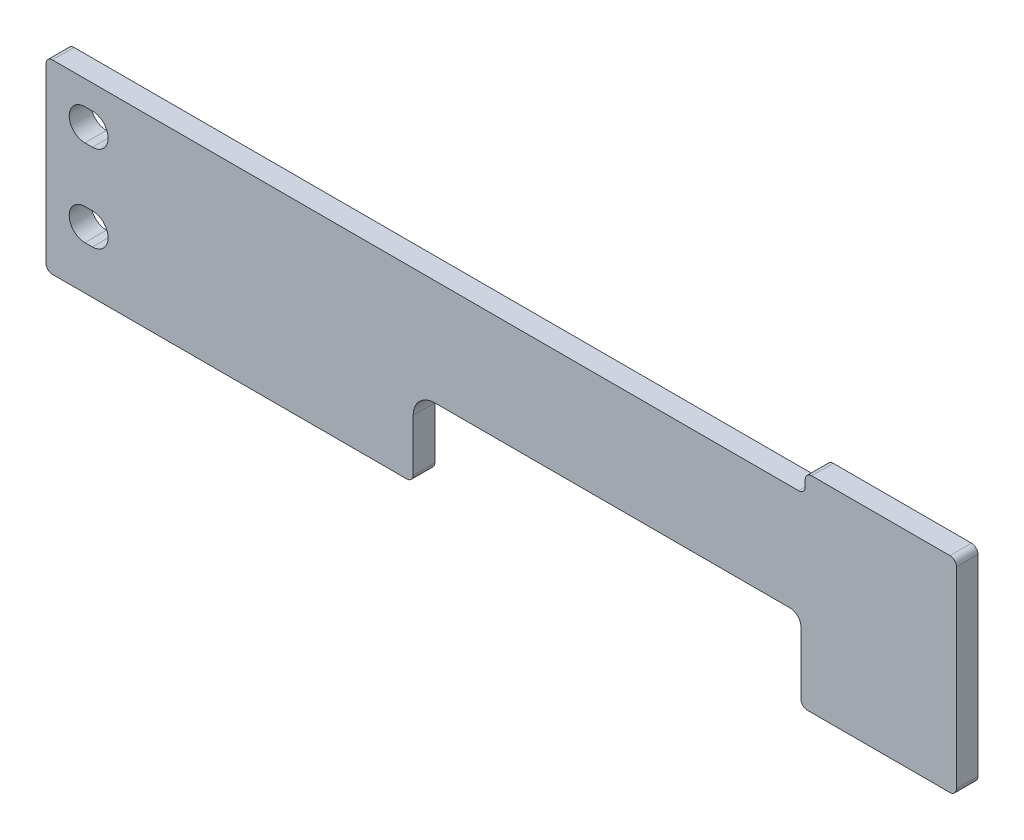
SolidWorks part; units mm, degrees
ref_plane "Plane1" through (0, 0, 0) normal (0, 0, 1) x (1, 0, 0)
ref_plane "Plane2" through (0, 0, 0) normal (0, 1, 0) x (1, 0, 0)
ref_plane "Plane3" through (0, 0, 0) normal (1, 0, 0) x (0, 0, -1)
sketch "Sketch1" plane through (0, 0, 0) normal (0, 0, 1) x (1, 0, 0)
  line L0 (-3, 0) -> (-67, 0)
  line L1 (-70, -3) -> (-70, -6)
  line L2 (-73, -9) -> (-418.5, -9)
  line L3 (-421.5, -12) -> (-421.5, -92)
  line L4 (-418.5, -95) -> (-254.5, -95)
  line L5 (-251.5, -92) -> (-251.5, -68)
  line L6 (-241.5, -58) -> (-77, -58)
  line L7 (0, -92) -> (0, -3)
  line L8 (-72, -63) -> (-72, -92)
  line L9 (-69, -95) -> (-3, -95)
  line L10 (-403.5, -74.75) -> (-400, -74.75)
  line L11 (-400, -60.25) -> (-403.5, -60.25)
  line L12 (-403.5, -34.75) -> (-400, -34.75)
  line L13 (-400, -20.25) -> (-403.5, -20.25)
  arc A0 (-400, -74.75) -> (-400, -60.25) centre (-400, -67.5) ccw
  arc A1 (-403.5, -60.25) -> (-403.5, -74.75) centre (-403.5, -67.5) ccw
  arc A2 (-400, -34.75) -> (-400, -20.25) centre (-400, -27.5) ccw
  arc A3 (-403.5, -20.25) -> (-403.5, -34.75) centre (-403.5, -27.5) ccw
  arc A4 (-418.5, -9) -> (-421.5, -12) centre (-418.5, -12) ccw
  arc A5 (-421.5, -92) -> (-418.5, -95) centre (-418.5, -92) ccw
  arc A6 (-254.5, -95) -> (-251.5, -92) centre (-254.5, -92) ccw
  arc A7 (-67, 0) -> (-70, -3) centre (-67, -3) ccw
  arc A8 (-70, -6) -> (-73, -9) centre (-73, -6) cw
  arc A9 (-3, 0) -> (0, -3) centre (-3, -3) cw
  arc A10 (-3, -95) -> (0, -92) centre (-3, -92) ccw
  arc A11 (-72, -92) -> (-69, -95) centre (-69, -92) ccw
  arc A12 (-251.5, -68) -> (-241.5, -58) centre (-241.5, -68) cw
  arc A13 (-77, -58) -> (-72, -63) centre (-77, -63) cw
  point P35 (0, 0)
  dimension "D9" = 7.25
  dimension "D12" = 18
  dimension "D14" = 3
  dimension "D15" = 10
  dimension "D16" = 5
  dimension "D1" = 421.5
  dimension "D3" = 9
  dimension "D4" = 170
  dimension "D5" = 72
  dimension "D6" = 95
  dimension "D7" = 37
  dimension "D8" = 18
  dimension "D10" = 40
  dimension "D11" = 27.5
  dimension "D13" = 70
extrude "Extrude1" add sketch "Sketch1" along normal blind 10
